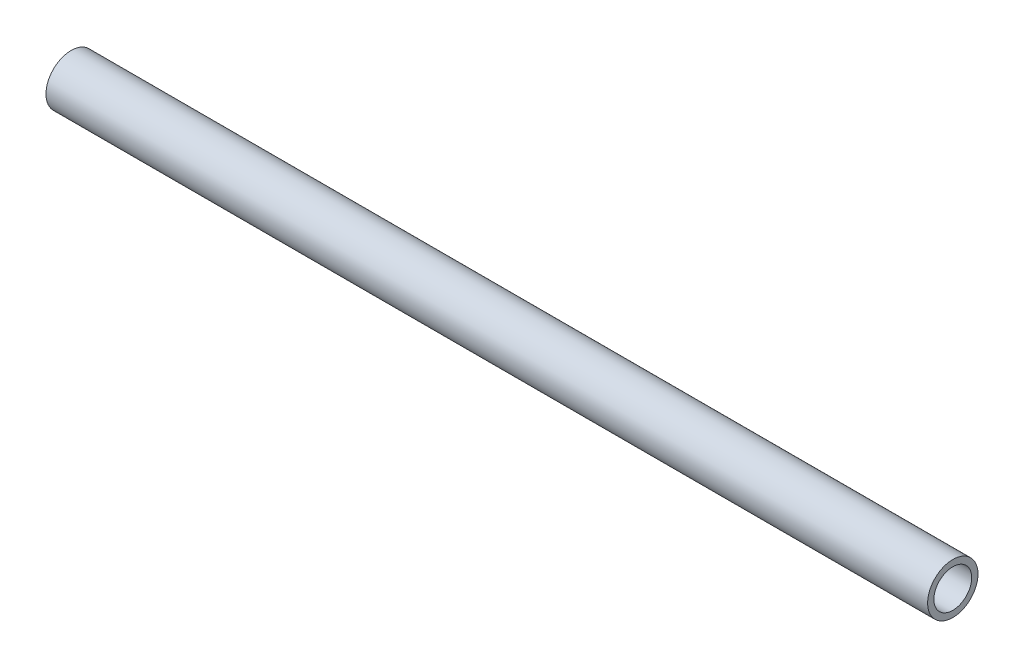
SolidWorks part; units mm, degrees
ref_plane "Front Plane" through (0, 0, 0) normal (0, 0, 1) x (1, 0, 0)
ref_plane "Top Plane" through (0, 0, 0) normal (0, 1, 0) x (1, 0, 0)
ref_plane "Right Plane" through (0, 0, 0) normal (1, 0, 0) x (0, 0, -1)
sketch "Sketch1" plane through (0, 0, 0) normal (1, 0, 0) x (0, 0, -1)
  circle A0 centre (0, 0) radius 8
  circle A1 centre (0, 0) radius 6
  dimension "D1" = 16
  dimension "D2" = 2
extrude "Boss-Extrude1" add sketch "Sketch1" along normal mid plane 280
